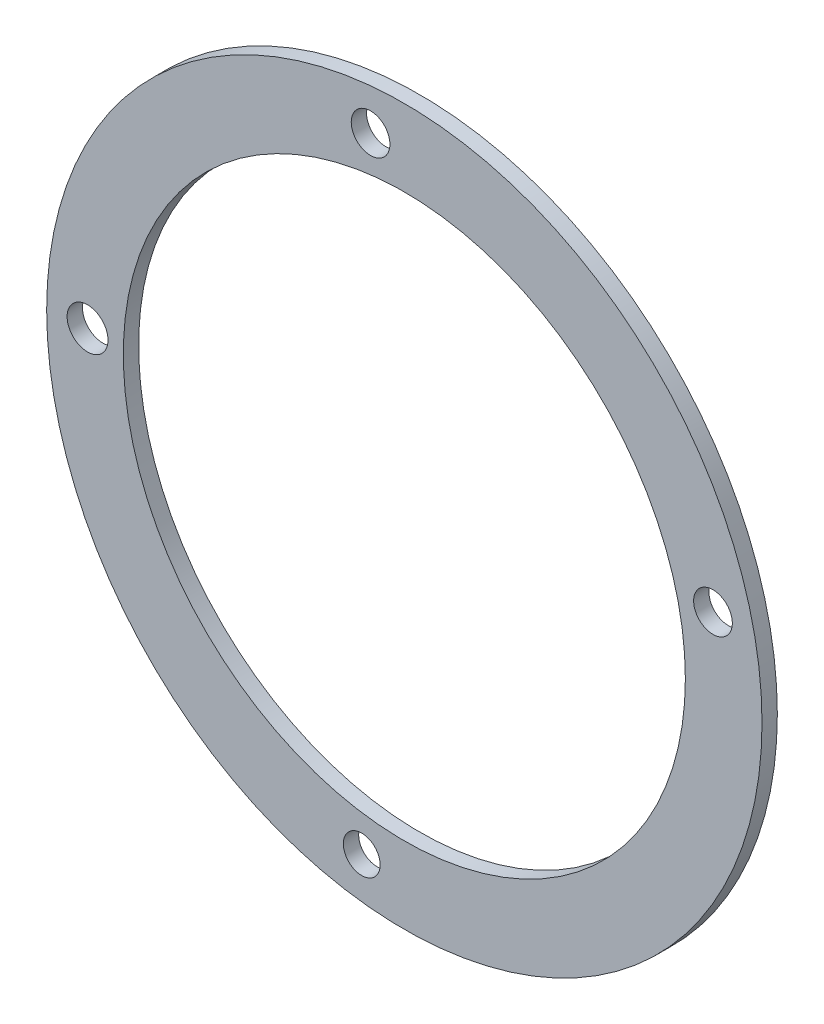
SolidWorks part; units mm, degrees
ref_plane "前视基准面" through (0, 0, 0) normal (0, 0, 1) x (1, 0, 0)
ref_plane "上视基准面" through (0, 0, 0) normal (0, 1, 0) x (1, 0, 0)
ref_plane "右视基准面" through (0, 0, 0) normal (1, 0, 0) x (0, 0, -1)
sketch "草图1" plane through (0, 0, 0) normal (0, 0, 1) x (1, 0, 0)
  circle A0 centre (0, 0) radius 55
  circle A1 centre (0, 0) radius 70
  dimension "D1" = 110
  dimension "D2" = 140
extrude "凸台-拉伸1" add sketch "草图1" along normal blind 3
sketch "草图2" plane through (0, 0, 0) normal (0, 0, -1) x (-1, 0, 0)
  circle A0 centre (61.9939, 0.8721) radius 4
  circle A1 centre (6.6068, 61.647) radius 3.7856
  circle A2 centre (-60.4011, 13.9893) radius 3.7856
  circle A3 centre (8.3383, -61.4367) radius 3.6
  circle A4 centre (8.3383, -61.4367) radius 3.6 construction
  circle A5 centre (-60.4011, 13.9893) radius 3.7856 construction
  circle A6 centre (6.6068, 61.647) radius 3.7856 construction
  circle A7 centre (61.9939, 0.8721) radius 4 construction
extrude "切除-拉伸1" cut sketch "草图2" against normal blind 3
